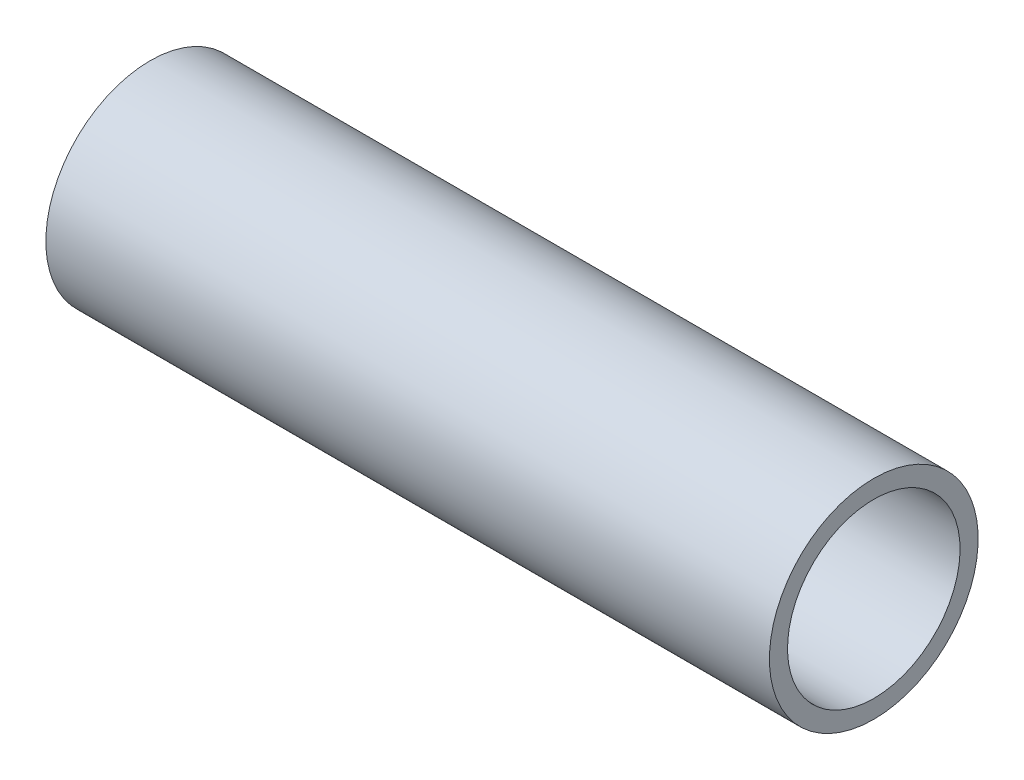
SolidWorks part; units mm, degrees
material "6061 Alloy"
ref_plane "Front Plane" through (0, 0, 0) normal (0, 0, 1) x (1, 0, 0)
ref_plane "Top Plane" through (0, 0, 0) normal (0, 1, 0) x (1, 0, 0)
ref_plane "Right Plane" through (0, 0, 0) normal (1, 0, 0) x (0, 0, -1)
sketch "Sketch3" plane through (0, 0, 0) normal (0, 0, 1) x (1, 0, 0)
  line L4 (66.04, 0) -> (0, 0)
  dimension "D1" = 66.04
ref_plane "Plane1" through (66.04, 0, 0) normal (-1, 0, 0) x (0, 0, 1)
sketch "Sketch4" plane through (66.04, 0, 0) normal (-1, 0, 0) x (0, 0, 1)
  circle A0 centre (0, 0) radius 9.525
  circle A1 centre (0, 0) radius 7.874
  dimension "D1" = 15.748
  dimension "D2" = 19.05
sweep "Sweep1" add profiles "Sketch4" path "Sketch3"
